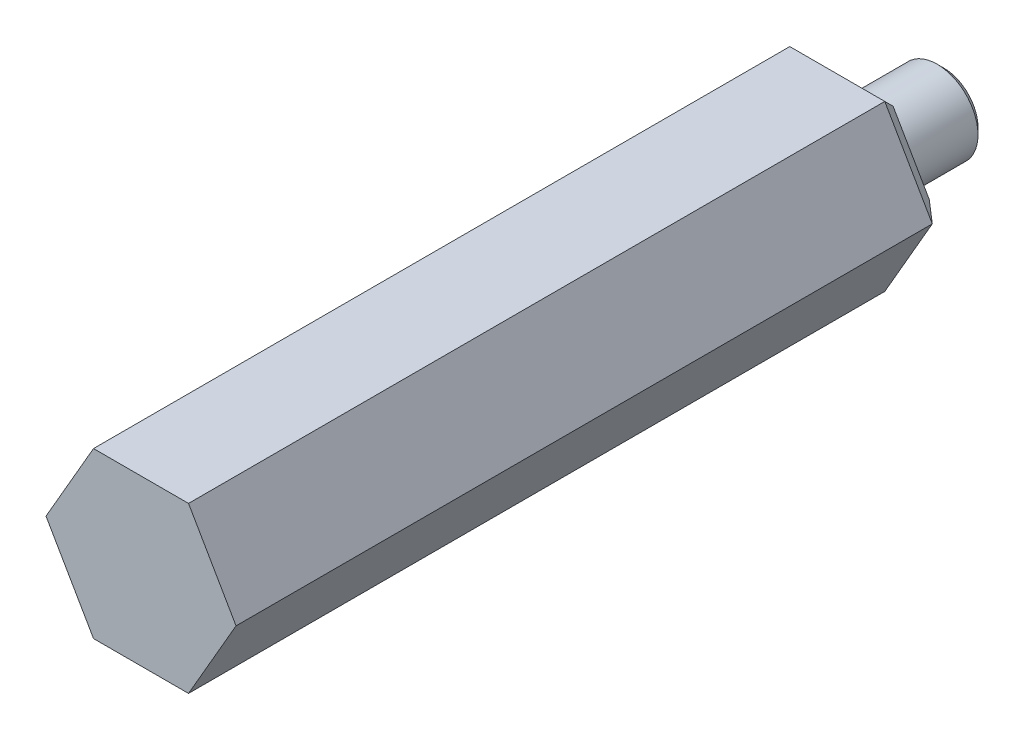
SolidWorks part; units mm, degrees
material "Alloy Steel"
ref_plane "Front Plane" through (0, 0, 0) normal (0, 0, 1) x (1, 0, 0)
ref_plane "Top Plane" through (0, 0, 0) normal (0, 1, 0) x (1, 0, 0)
ref_plane "Right Plane" through (0, 0, 0) normal (1, 0, 0) x (0, 0, -1)
sketch "Sketch1" plane through (0, 0, 0) normal (0, 1, 0) x (1, 0, 0)
  line L0 (7.366, -27.7495) -> (7.366, 27.7495)
  line L1 (7.366, 27.7495) -> (3.1623, 27.7495)
  line L2 (3.1623, 27.7495) -> (3.1623, 34.4805)
  line L3 (0, 34.4805) -> (0, -27.7495)
  line L4 (3.1623, 34.4805) -> (0, 34.4805)
  line L5 (0, 0) -> (7.366, 0) construction
  line L6 (7.366, -27.7495) -> (0, -27.7495)
  line L16 (0, -27.7495) -> (0, 34.4805) construction
  dimension "D1" = 62.23
  dimension "D2" = 14.732
  dimension "D3" = 6.731
  dimension "D4" = 6.3246
  dimension "D5" = 55.499
revolve "Revolve1" add sketch "Sketch1" angle 360 about L3
chamfer "Chamfer1" distance 0.508 angle 45 1 edges at (-3.1623, 0, -34.4805)
sketch "Sketch2" plane through (0, 0, -27.7495) normal (0, 0, -1) x (-1, 0, 0)
  line L0 (-7.366, 0) -> (7.366, 0) construction
  line L1 (-7.366, 0) -> (-3.683, -6.3791)
  line L2 (-3.683, -6.3791) -> (3.683, -6.3791)
  line L3 (3.683, -6.3791) -> (7.366, 0)
  line L4 (7.366, 0) -> (3.683, 6.3791)
  line L5 (3.683, 6.3791) -> (-3.683, 6.3791)
  line L6 (-3.683, 6.3791) -> (-7.366, 0)
  circle A0 centre (0, 0) radius 6.3791 construction
  circle A1 centre (0, 0) radius 7.366 construction
  circle A2 centre (0, 0) radius 7.366
  circle M2 centre (0, 0) radius 7.366
extrude "Extrude1" cut sketch "Sketch2" against normal up to next contours L5 M2 | L4 M2 | L3 M2 | L2 M2 | L1 M2 | L6 M2
chamfer "Chamfer2" distance 1.524 angle 45 6 edges at (5.5245, 3.1896, -27.7495) (5.5245, -3.1896, -27.7495) (0, -6.3791, -27.7495) (-5.5245, -3.1896, -27.7495) (-5.5245, 3.1896, -27.7495) (0, 6.3791, -27.7495)
